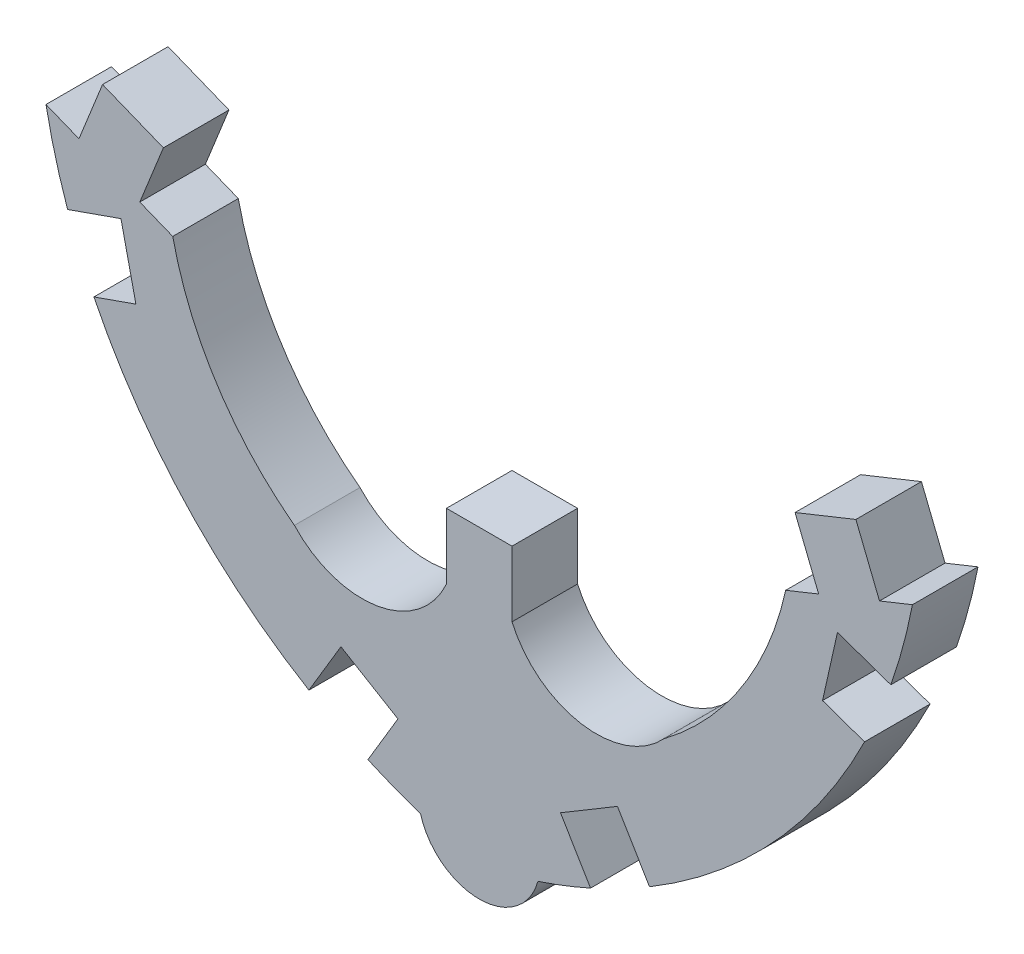
SolidWorks part; units mm, degrees
ref_plane "Front Plane" through (0, 0, 0) normal (0, 0, 1) x (1, 0, 0)
ref_plane "Top Plane" through (0, 0, 0) normal (0, 1, 0) x (1, 0, 0)
ref_plane "Right Plane" through (0, 0, 0) normal (1, 0, 0) x (0, 0, -1)
sketch "Sketch1" plane through (0, 0, 0) normal (0, 0, 1) x (1, 0, 0)
  line L0 (106.8002, 0) -> (106.8002, -1.524)
  line L1 (100.4376, 2.2927) -> (99.6715, 2.6002)
  line L2 (98.2572, 3.1679) -> (97.4911, 3.4753)
  line L3 (99.6715, 2.6002) -> (100.2201, 3.967)
  line L4 (98.2572, 3.1679) -> (98.8057, 4.5346)
  line L5 (106.8002, 0) -> (108.3242, 0)
  line L6 (100.2201, 3.967) -> (98.8057, 4.5346)
  line L7 (117.1308, 1.6119) -> (115.8905, 2.0478)
  line L8 (116.5194, 0.1576) -> (115.5434, 0.5006)
  line L9 (114.9042, 3.967) -> (116.3186, 4.5346)
  line L10 (116.8671, 3.1679) -> (116.3186, 4.5346)
  line L11 (115.4528, 2.6002) -> (114.9042, 3.967)
  line L12 (116.8671, 3.1679) -> (117.6332, 3.4753)
  line L13 (114.6867, 2.2927) -> (115.4528, 2.6002)
  line L14 (108.3242, 0) -> (108.3242, -1.524)
  line L15 (115.5434, 0.5006) -> (115.8905, 2.0478)
  line L16 (111.5209, -5.2597) -> (110.7768, -4.013)
  line L17 (110.1493, -5.973) -> (109.4516, -4.8041)
  line L18 (109.4516, -4.8041) -> (110.7768, -4.013)
  line L19 (107.5622, -6.071) -> (107.5622, 5.5011) construction
  line L20 (104.975, -5.973) -> (105.6728, -4.8041)
  line L21 (105.6728, -4.8041) -> (104.3475, -4.013)
  line L22 (103.6034, -5.2597) -> (104.3475, -4.013)
  line L23 (98.6049, 0.1576) -> (99.5809, 0.5006)
  line L24 (99.5809, 0.5006) -> (99.2338, 2.0478)
  line L25 (97.9935, 1.6119) -> (99.2338, 2.0478)
  arc A0 (106.8002, -1.524) -> (103.2661, -2.1101) centre (104.8411, -0.659) cw
  arc A1 (103.2661, -2.1101) -> (100.4376, 2.2927) centre (107.7987, 3.9118) cw
  arc A2 (97.4911, 3.4753) -> (97.9935, 1.6119) centre (110.2929, 5.9274) ccw
  arc A3 (117.6332, 3.4753) -> (117.1308, 1.6119) centre (104.8315, 5.9274) cw
  arc A4 (111.8582, -2.1101) -> (114.6867, 2.2927) centre (107.3256, 3.9118) ccw
  arc A5 (108.3242, -1.524) -> (111.8582, -2.1101) centre (110.2832, -0.659) ccw
  arc A6 (106.1972, -6.447) -> (108.9271, -6.447) centre (107.5622, -6.071) ccw
  arc A7 (116.5194, 0.1576) -> (111.5209, -5.2597) centre (104.8315, 5.9274) cw
  arc A8 (110.1493, -5.973) -> (108.9271, -6.447) centre (104.8315, 5.9274) cw
  arc A9 (104.975, -5.973) -> (106.1972, -6.447) centre (110.2929, 5.9274) ccw
  arc A10 (98.6049, 0.1576) -> (103.6034, -5.2597) centre (110.2929, 5.9274) ccw
extrude "Boss-Extrude1" add sketch "Sketch1" along normal blind 1.524
